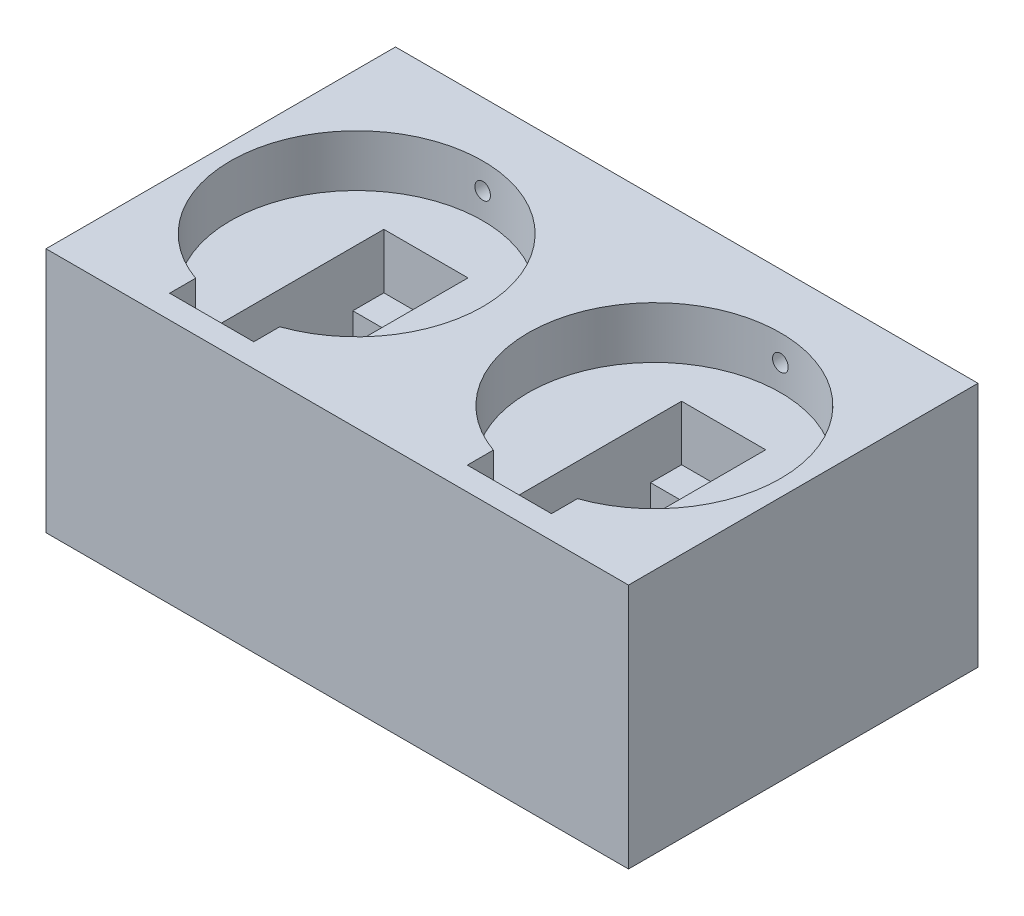
SolidWorks part; units mm, degrees
ref_plane "Front Plane" through (0, 0, 0) normal (0, 0, 1) x (1, 0, 0)
ref_plane "Top Plane" through (0, 0, 0) normal (0, 1, 0) x (1, 0, 0)
ref_plane "Right Plane" through (0, 0, 0) normal (1, 0, 0) x (0, 0, -1)
sketch "Sketch1" plane through (0, 0, 0) normal (0, 1, 0) x (1, 0, 0)
  line L1 (45, -27) -> (-45, -27)
  line L2 (45, -27) -> (45, 27)
  line L3 (45, 27) -> (-45, 27)
  line L4 (-45, -27) -> (-45, 27)
  line L5 (45, -27) -> (-45, 27) construction
  line L6 (45, 27) -> (-45, -27) construction
  point P0 (0, 0)
  dimension "D1" = 54
  dimension "D2" = 90
extrude "Boss-Extrude1" add sketch "Sketch1" along normal blind 38
sketch "Sketch2" plane through (-45, 0, 0) normal (-1, 0, 0) x (0, 0, 1)
  line L0 (-4.9, 2.5) -> (18.6, 2.5)
  line L1 (18.6, 2.5) -> (18.6, 21.5)
  line L2 (18.6, 21.5) -> (23.4, 21.5)
  line L3 (23.4, 21.5) -> (23.4, 24)
  line L4 (23.4, 24) -> (18.6, 24)
  line L5 (18.6, 24) -> (18.6, 37.4024)
  line L6 (18.6, 37.4024) -> (-4.9, 37.4024)
  line L7 (-4.9, 37.4024) -> (-4.9, 24)
  line L8 (-4.9, 24) -> (-9.7, 24)
  line L9 (-9.7, 24) -> (-9.7, 21.5)
  line L10 (-9.7, 21.5) -> (-4.9, 21.5)
  line L11 (-4.9, 21.5) -> (-4.9, 2.5)
  line L12 (-4.9, 25.3) -> (18.6, 25.3) construction
  line L14 (27, 38) -> (-27, 38) construction
  line L15 (0, -55) -> (0, 55) construction
  point P14 (1, 37.4024)
  dimension "D1" = 23.5
  dimension "D2" = 19
  dimension "D3" = 2.5
  dimension "D4" = 4.8
  dimension "D5" = 22.8
  dimension "D6" = 5.9
  dimension "D7" = 14
  dimension "D8" = 1
extrude "Cut-Extrude1" cut sketch "Sketch2" against normal blind 13 from offset 15.5 offset against normal yes
sketch "Sketch3" plane through (0, 38, 0) normal (0, 1, 0) x (1, 0, 0)
  line L0 (-45, 27) -> (-45, -27) construction
  line L1 (-45, -1) -> (0, -1) construction
  line L2 (0, -55) -> (0, 55) construction
  circle A0 centre (-23, -1) radius 19.5
  point P0 (-45, -1)
  dimension "D1" = 39
  dimension "D2" = 22
sketch "Sketch4" plane through (0, 24, 0) normal (0, -1, 0) x (1, 0, 0)
  line L4 (-29.5, 23.4) -> (-29.5, 18.6)
  line L5 (-29.5, 18.6) -> (-16.5, 18.6)
  line L6 (-16.5, 18.6) -> (-16.5, 23.4)
  line L7 (-16.5, 23.4) -> (-29.5, 23.4)
  line L8 (-29.5, 23.4) -> (-29.5, 18.6)
  line L9 (-29.5, 18.6) -> (-16.5, 18.6)
  line L10 (-16.5, 18.6) -> (-16.5, 23.4)
  line L11 (-16.5, 23.4) -> (-29.5, 23.4)
  line L12 (-29.5, -4.9) -> (-29.5, -9.7)
  line L13 (-29.5, -9.7) -> (-16.5, -9.7)
  line L14 (-16.5, -9.7) -> (-16.5, -4.9)
  line L15 (-16.5, -4.9) -> (-29.5, -4.9)
  line L16 (-29.5, -4.9) -> (-29.5, -9.7)
  line L17 (-29.5, -9.7) -> (-16.5, -9.7)
  line L18 (-16.5, -9.7) -> (-16.5, -4.9)
  line L19 (-16.5, -4.9) -> (-29.5, -4.9)
  dimension "D1" = 0
  dimension "D2" = 0
extrude "Cut-Extrude2" cut sketch "Sketch4" against normal up to surface (14 mm away) up to face at (0, 38, 0)
extrude "Cut-Extrude3" cut sketch "Sketch3" against normal blind 8
sketch "Sketch7" plane through (0, 21.5, 0) normal (0, 1, 0) x (1, 0, 0)
  line L0 (-29.5, -18.6) -> (-29.5, -23.4) construction
  line L1 (-29.5, -23.4) -> (-16.5, -23.4) construction
  line L2 (-16.5, -23.4) -> (-16.5, -18.6) construction
  line L3 (-16.5, -18.6) -> (-29.5, -18.6) construction
  line L4 (-29.5, 9.7) -> (-29.5, 4.9) construction
  line L5 (-29.5, 4.9) -> (-16.5, 4.9) construction
  line L6 (-16.5, 4.9) -> (-16.5, 9.7) construction
  line L7 (-16.5, 9.7) -> (-29.5, 9.7) construction
  line L8 (-29.5, -18.6) -> (-29.5, -23.4) construction
  line L9 (-29.5, -23.4) -> (-16.5, -23.4) construction
  line L10 (-16.5, -23.4) -> (-16.5, -18.6) construction
  line L11 (-16.5, -18.6) -> (-29.5, -18.6) construction
  line L12 (-29.5, 9.7) -> (-29.5, 4.9) construction
  line L13 (-29.5, 4.9) -> (-16.5, 4.9) construction
  line L14 (-16.5, 4.9) -> (-16.5, 9.7) construction
  line L15 (-16.5, 9.7) -> (-29.5, 9.7) construction
  circle A0 centre (-23, 7.5078) radius 1.5
  circle A1 centre (-23, -19.2554) radius 1.5
  point P12 (-23, 9.7)
  point P15 (-23, -20.6795)
  dimension "D1" = 3
  dimension "D2" = 3
extrude "Cut-Extrude4" cut sketch "Sketch7" against normal blind 5
mirror "Mirror1" about plane through (0, 0, 0) normal (1, 0, 0) of "Cut-Extrude4", "Cut-Extrude3", "Cut-Extrude2", "Cut-Extrude1"
sketch "Sketch8" plane through (0, 0, -27) normal (0, 0, -1) x (-1, 0, 0)
  line L0 (42.5, 38) -> (3.5, 38) construction
  line L1 (42.5, 38) -> (3.5, 38) construction
  line L2 (16.5, 30) -> (16.5, 38) construction
  line L3 (29.5, 30) -> (29.5, 38) construction
  line L4 (16.5, 30) -> (16.5, 38) construction
  line L5 (29.5, 30) -> (29.5, 38) construction
  line L6 (16.5, 34) -> (29.5, 34) construction
  circle A0 centre (23, 34) radius 2.4
  point P11 (23, 34)
  dimension "D1" = 4.8
sketch "Sketch9" plane through (0, 0, -27) normal (0, 0, -1) x (-1, 0, 0)
  line L0 (-3.5, 38) -> (-42.5, 38) construction
  line L1 (-3.5, 38) -> (-42.5, 38) construction
  line L2 (-29.5, 30) -> (-29.5, 38) construction
  line L3 (-16.5, 30) -> (-16.5, 38) construction
  line L4 (-29.5, 30) -> (-29.5, 38) construction
  line L5 (-16.5, 30) -> (-16.5, 38) construction
  line L6 (-29.5, 34) -> (-16.5, 34) construction
  circle A0 centre (-23, 34) radius 2.4
  point P11 (-23, 34)
  dimension "D1" = 4.8
hole_wizard "M5x0.8 Tapped Hole1" positions "3DSketch1" profile "Sketch10" tap size "M5x0.8" standard "ANSI Metric"
sketch3d "3DSketch1"
  point P0 (23, 34, -27)
  point P3 (-23, 34, -27)
sketch "Sketch10" plane through (23, 34, -27) normal (1, 0, 0) x (0, 1, 0)
  line L0 (0, 0) -> (0, 9.2618)
  line L1 (0, 9.2618) -> (2.1, 8)
  line L2 (2.1, 8) -> (2.1, 0.9)
  line L3 (2.1, 0.9) -> (3, 0)
  line L5 (3, 0) -> (0, 0)
  line L6 (-2.1, 0.9) -> (-3, 0) construction
  line L10 (0, 9.2618) -> (-2.1, 8) construction
  line L11 (0, -6.35) -> (0, 107.95) construction
  dimension "Tap Drill Dia." = 4.2
  dimension "Tap Drill Depth" = 8
  dimension "Near C'Sink Dia." = 6
  dimension "Near C'Sink Angle" = 90
  dimension "Drill Angle" = 118
cosmetic thread "Hole Thread1" parameters "D1"=10, "D2"=5
cosmetic thread "Hole Thread2" parameters "D1"=10, "D2"=5
sketch "Sketch11" plane through (45, 0, 0) normal (1, 0, 0) x (0, 0, -1)
  line L1 (7.4247, 19.2413) -> (25.7147, 19.2413)
  line L2 (7.4247, 19.2413) -> (7.4247, 1.4813)
  line L3 (7.4247, 1.4813) -> (25.7147, 1.4813)
  line L4 (25.7147, 19.2413) -> (25.7147, 1.4813)
  dimension "D1" = 18.29
  dimension "D2" = 17.76
